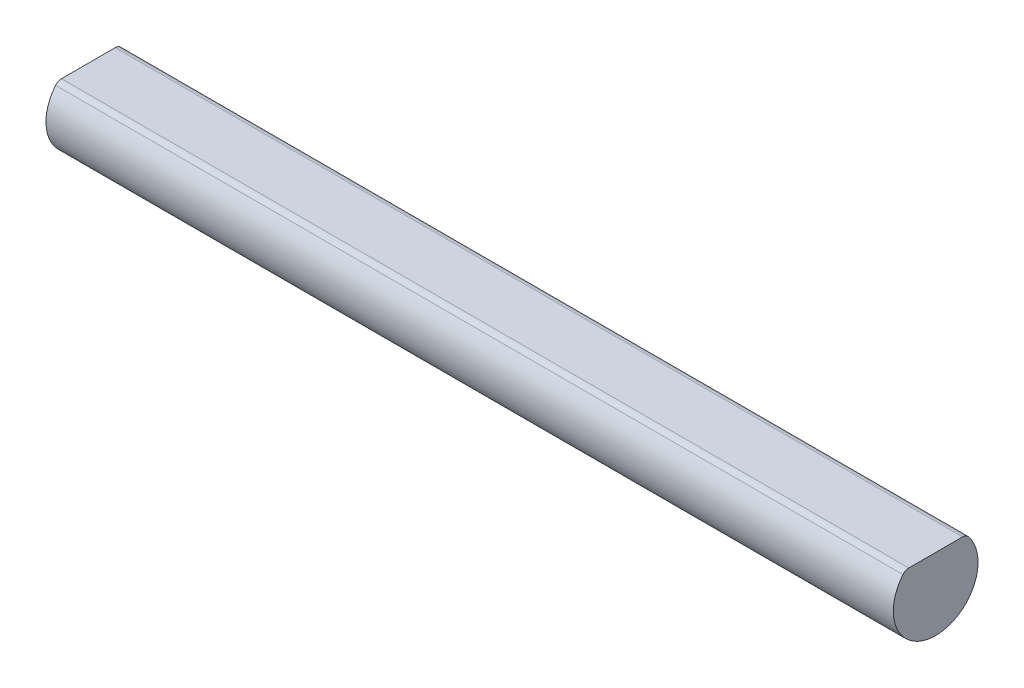
SolidWorks part; units mm, degrees
ref_plane "Front Plane" through (0, 0, 0) normal (0, 0, 1) x (1, 0, 0)
ref_plane "Top Plane" through (0, 0, 0) normal (0, 1, 0) x (1, 0, 0)
ref_plane "Right Plane" through (0, 0, 0) normal (1, 0, 0) x (0, 0, -1)
sketch "Sketch1" plane through (0, 0, 0) normal (1, 0, 0) x (0, 0, -1)
  circle A0 centre (0, 0) radius 5
  dimension "D1" = 10
extrude "Boss-Extrude1" add sketch "Sketch1" along normal blind 100
sketch "Sketch2" plane through (100, 0, 0) normal (1, 0, 0) x (0, 0, -1)
  line L0 (0, 5.5) -> (0, -5.5) construction
  line L2 (0, 3.5) -> (-5.7401, 3.5)
  line L3 (0, 3.5) -> (0, 5.9002)
  line L4 (0, 5.9002) -> (-5.7401, 5.9002)
  line L5 (-5.7401, 3.5) -> (-5.7401, 5.9002)
  line L6 (0, 3.5) -> (4.4272, 3.5)
  line L7 (0, 3.5) -> (0, 5.9002)
  line L8 (0, 5.9002) -> (4.4272, 5.9002)
  line L9 (4.4272, 3.5) -> (4.4272, 5.9002)
  circle A0 centre (0, 0) radius 5 construction
  point P0 (0, 3.5)
  point P1 (0, 5)
  circle M4 centre (0, 0) radius 5
  dimension "D1" = 1.5
extrude "Cut-Extrude1" cut sketch "Sketch2" against normal through all contours L2 L3 M4 | L3 L6 M4 | L6 L9 L8 L3 M4 | L5 L2 L3 L4 M4
fillet "Fillet1" radius 0.9 2 edges at (50, 3.5, -3.5707) (50, 3.5, 3.5707)
